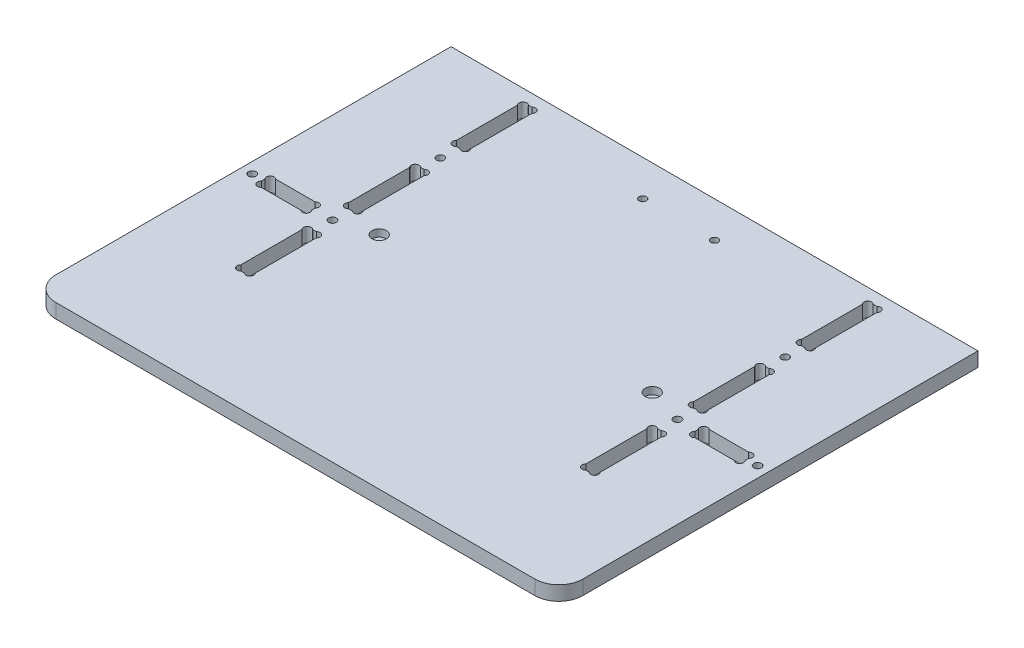
SolidWorks part; units mm, degrees
ref_plane "Plan de face" through (0, 0, 0) normal (0, 0, 1) x (1, 0, 0)
ref_plane "Plan de dessus" through (0, 0, 0) normal (0, 1, 0) x (1, 0, 0)
ref_plane "Plan de droite" through (0, 0, 0) normal (1, 0, 0) x (0, 0, -1)
sketch "Esquisse2" plane through (0, 0, 0) normal (0, 1, 0) x (1, 0, 0)
  line L0 (-40.8344, 65) -> (14.2855, 65) construction
  line L1 (0, 0) -> (160, 0) construction
  line L2 (0, 0) -> (0, 130) construction
  line L3 (0, 130) -> (160, 130) construction
  line L4 (160, 0) -> (160, 130) construction
  line L5 (80, 138.5727) -> (80, -10.0112) construction
  line L6 (5, 135.8712) -> (5, -2.4469) construction
  line L7 (11, 135.8712) -> (11, -2.4469) construction
  line L8 (-6.6063, 125) -> (16.2666, 125) construction
  line L9 (-6.6063, 95) -> (14.2855, 95) construction
  line L10 (2.2186, 87.5) -> (10.8635, 87.5) construction
  line L11 (-5.1655, 80) -> (14.2855, 80) construction
  line L12 (8, 98.5901) -> (8, 83.9707) construction
  line L13 (2.2186, 110) -> (14.2855, 110) construction
  line L14 (5, 125) -> (21.8611, 108.1389) construction
  line L15 (7.2627, 125) -> (8.7373, 125)
  line L16 (11, 122.7373) -> (11, 97.2627)
  line L17 (8.7373, 95) -> (7.2627, 95)
  line L18 (5, 97.2627) -> (5, 122.7373)
  line L19 (7.2627, 80) -> (8.7373, 80)
  line L20 (7.2627, 50) -> (8.7373, 50)
  line L21 (8.7373, 35) -> (7.2627, 35)
  line L22 (5, 32.7373) -> (5, 7.2627)
  line L23 (11, 7.2627) -> (11, 32.7373)
  line L24 (7.2627, 5) -> (8.7373, 5)
  line L25 (5, 77.7373) -> (5, 52.2627)
  line L26 (11, 52.2627) -> (11, 77.7373)
  line L27 (152.7373, 5) -> (151.2627, 5)
  line L28 (155, 32.7373) -> (155, 7.2627)
  line L29 (149, 7.2627) -> (149, 32.7373)
  line L30 (151.2627, 35) -> (152.7373, 35)
  line L31 (155, 77.7373) -> (155, 52.2627)
  line L32 (149, 52.2627) -> (149, 77.7373)
  line L33 (152.7373, 50) -> (151.2627, 50)
  line L34 (152.7373, 80) -> (151.2627, 80)
  line L35 (151.2627, 95) -> (152.7373, 95)
  line L36 (155, 97.2627) -> (155, 122.7373)
  line L37 (149, 122.7373) -> (149, 97.2627)
  line L38 (152.7373, 125) -> (151.2627, 125)
  line L39 (-20, -45) -> (180, -45)
  line L40 (-30, 130) -> (190, 130)
  line L41 (-30, 130) -> (-30, -35)
  line L42 (-21, 53.7406) -> (-21, 30.6623) construction
  line L43 (23, 80.9657) -> (23, 16.2308) construction
  line L44 (14.2855, 5) -> (145.3344, 5) construction
  line L45 (145.3344, 85) -> (14.2855, 85) construction
  line L46 (167.2289, 47) -> (-33.5392, 47) construction
  line L47 (212.1831, 42.5) -> (-40.0739, 42.5) construction
  line L48 (-61.9181, 0) -> (207.7659, 0) construction
  line L49 (-30, -56.3976) -> (-30, 135.8712) construction
  line L51 (190, 130) -> (190, -35)
  line L52 (-31.7937, 39.5) -> (7.2627, 39.5) construction
  line L53 (-31.7937, 45.5) -> (3.2216, 45.5) construction
  line L54 (-21, 45.5) -> (-9.6603, 34.1603) construction
  line L55 (-10.5, 36.8014) -> (-10.5, 48.3974) construction
  line L56 (-25.5, 44.0604) -> (-25.5, 36.0648) construction
  line L58 (181, 41.7627) -> (181, 43.2373)
  line L59 (-2.2627, 39.5) -> (-18.7373, 39.5)
  line L60 (0, 41.7627) -> (0, 43.2373)
  line L61 (-2.2627, 45.5) -> (-18.7373, 45.5)
  line L63 (-21, 41.7627) -> (-21, 43.2373)
  line L64 (162.2627, 39.5) -> (178.7373, 39.5)
  line L65 (162.2627, 45.5) -> (178.7373, 45.5)
  line L66 (160, 41.7627) -> (160, 43.2373)
  line L68 (54.313, 115) -> (110.9821, 115) construction
  line L69 (70, 62.6311) -> (70, 30.6623) construction
  line L70 (65, 117.8715) -> (65, 107.0067) construction
  line L71 (-61.9181, -45) -> (207.7659, -45) construction
  line L72 (95.9898, 45.4) -> (66.0104, 45.4) construction
  line L73 (190, 135.8712) -> (190, -54.1234) construction
  line L74 (66.0104, 48.6) -> (95.9898, 48.6) construction
  line L75 (72.0173, 81) -> (100.0085, 81) construction
  line L76 (207.7659, 130) -> (-48.9597, 130) construction
  arc A0 (7.2627, 125) -> (5, 122.7373) centre (6.1314, 123.8686) ccw
  arc A1 (8.7373, 125) -> (11, 122.7373) centre (9.8686, 123.8686) cw
  arc A2 (7.2627, 95) -> (5, 97.2627) centre (6.1314, 96.1314) cw
  arc A3 (8.7373, 95) -> (11, 97.2627) centre (9.8686, 96.1314) ccw
  arc A4 (7.2627, 80) -> (5, 77.7373) centre (6.1314, 78.8686) ccw
  arc A5 (8.7373, 80) -> (11, 77.7373) centre (9.8686, 78.8686) cw
  arc A6 (7.2627, 50) -> (5, 52.2627) centre (6.1314, 51.1314) cw
  arc A7 (8.7373, 50) -> (11, 52.2627) centre (9.8686, 51.1314) ccw
  arc A8 (8.7373, 35) -> (11, 32.7373) centre (9.8686, 33.8686) cw
  arc A9 (7.2627, 35) -> (5, 32.7373) centre (6.1314, 33.8686) ccw
  arc A10 (8.7373, 5) -> (11, 7.2627) centre (9.8686, 6.1314) ccw
  arc A11 (7.2627, 5) -> (5, 7.2627) centre (6.1314, 6.1314) cw
  arc A12 (151.2627, 5) -> (149, 7.2627) centre (150.1314, 6.1314) cw
  arc A13 (152.7373, 5) -> (155, 7.2627) centre (153.8686, 6.1314) ccw
  arc A14 (151.2627, 35) -> (149, 32.7373) centre (150.1314, 33.8686) ccw
  arc A15 (152.7373, 35) -> (155, 32.7373) centre (153.8686, 33.8686) cw
  arc A16 (151.2627, 50) -> (149, 52.2627) centre (150.1314, 51.1314) cw
  arc A17 (152.7373, 50) -> (155, 52.2627) centre (153.8686, 51.1314) ccw
  arc A18 (152.7373, 80) -> (155, 77.7373) centre (153.8686, 78.8686) cw
  arc A19 (151.2627, 80) -> (149, 77.7373) centre (150.1314, 78.8686) ccw
  arc A20 (151.2627, 95) -> (149, 97.2627) centre (150.1314, 96.1314) cw
  arc A21 (152.7373, 95) -> (155, 97.2627) centre (153.8686, 96.1314) ccw
  arc A22 (151.2627, 125) -> (149, 122.7373) centre (150.1314, 123.8686) ccw
  arc A23 (152.7373, 125) -> (155, 122.7373) centre (153.8686, 123.8686) cw
  circle A24 centre (8, 87.5) radius 1.6
  circle A25 centre (8, 42.5) radius 1.6
  circle A26 centre (152, 42.5) radius 1.6
  circle A27 centre (152, 87.5) radius 1.6
  arc A28 (-30, -35) -> (-20, -45) centre (-20, -35) ccw
  arc A29 (180, -45) -> (190, -35) centre (180, -35) ccw
  arc A31 (-18.7373, 45.5) -> (-21, 43.2373) centre (-19.8686, 44.3686) ccw
  circle A32 centre (-25.5, 42.5) radius 1.6
  arc A33 (-18.7373, 39.5) -> (-21, 41.7627) centre (-19.8686, 40.6314) cw
  arc A34 (-2.2627, 45.5) -> (0, 43.2373) centre (-1.1314, 44.3686) cw
  arc A35 (-2.2627, 39.5) -> (0, 41.7627) centre (-1.1314, 40.6314) ccw
  circle A36 centre (185.5, 42.5) radius 1.6
  arc A37 (178.7373, 45.5) -> (181, 43.2373) centre (179.8686, 44.3686) cw
  arc A38 (178.7373, 39.5) -> (181, 41.7627) centre (179.8686, 40.6314) ccw
  arc A39 (162.2627, 45.5) -> (160, 43.2373) centre (161.1314, 44.3686) ccw
  arc A40 (162.2627, 39.5) -> (160, 41.7627) centre (161.1314, 40.6314) cw
  point P187 (-30, 0)
  point P190 (190, 0)
  dimension "D10" = 12
  dimension "D11" = 3
  dimension "D17" = 15
  dimension "D19" = 10
  dimension "D18" = 10
  dimension "D22" = 34
  dimension "D1" = 5
  dimension "D2" = 5
  dimension "D3" = 6
  dimension "D4" = 3
  dimension "D5" = 30
  dimension "D6" = 15
  dimension "D7" = 45
  dimension "D8" = 15
  dimension "D9" = 7.5
  dimension "D12" = 6
  dimension "D13" = 21
  dimension "D14" = 10.5
  dimension "D15" = 45
  dimension "D16" = 4.5
  dimension "D20" = 1.6
  dimension "D21" = 3.2
  dimension "D23" = 110
extrude "Extrusion1" add sketch "Esquisse2" along normal blind 6
sketch "Esquisse4" plane through (0, 6, 0) normal (0, 1, 0) x (-1, 0, 0)
  line L0 (-80, -138.2004) -> (-80, 10.3402) construction
  line L1 (-14.6457, -47) -> (-146.6025, -47) construction
  line L2 (-51.7363, -115) -> (-126.4524, -115) construction
  line L3 (-65, -121.6166) -> (-65, -105.5678) construction
  line L4 (-23, -57.4214) -> (-23, -40.1244) construction
  circle A0 centre (-65, -115) radius 1.53
  circle A1 centre (-23, -47) radius 3
  circle A2 centre (-95, -115) radius 1.53
  circle A3 centre (-137, -47) radius 3
  dimension "D1" = 15
extrude "Enlèv. mat.-Extru.1" cut sketch "Esquisse4" against normal blind 3
